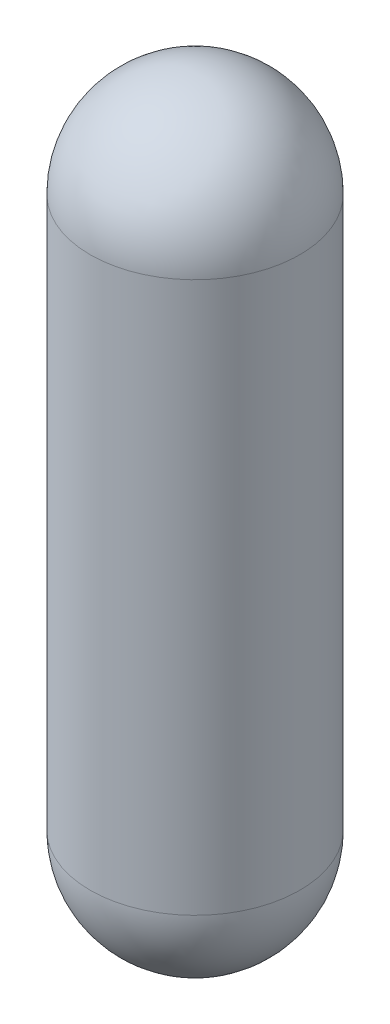
SolidWorks part; units mm, degrees
ref_plane "Front" through (0, 0, 0) normal (0, 0, 1) x (1, 0, 0)
ref_plane "Top" through (0, 0, 0) normal (0, 1, 0) x (1, 0, 0)
ref_plane "Right" through (0, 0, 0) normal (1, 0, 0) x (0, 0, -1)
sketch "Sketch1" plane through (0, 0, 0) normal (0, 1, 0) x (1, 0, 0)
  circle A0 centre (0, 0) radius 50.8
  dimension "D1" = 101.6
extrude "Extrude1" add sketch "Sketch1" along normal blind 266.7
sketch "Sketch2" plane through (0, 266.7, 0) normal (0, 1, 0) x (-1, 0, 0)
  circle A0 centre (0, 0) radius 50.8 construction
  point P0 (0, 0)
sketch "Sketch5" plane through (0, 0, 0) normal (1, 0, 0) x (0, 0, -1)
  line L0 (0, 0) -> (-50.8, 0)
  line L1 (0, 0) -> (0, -50.8)
  line L2 (0, 317.5) -> (0, 266.7)
  line L3 (0, 266.7) -> (-50.8, 266.7)
  line L4 (0, 266.7) -> (0, 0) construction
  arc A0 (-50.8, 0) -> (0, -50.8) centre (0, 0) ccw
  arc A1 (-50.8, 266.7) -> (0, 317.5) centre (0, 266.7) cw
revolve "Revolve1" add sketch "Sketch5" angle 360 about L4
sketch3d "3DSketch1"
  line L0 (0, 0, 0) -> (0, -80.2221, 0) construction
  circle A0 centre (0, 0, 0) radius 50.8 construction
  point P3 (0, -50.8, 0)
  point P4 (-18.0698, 0, 47.4776)
  point P7 (0, 50.8, 0)
